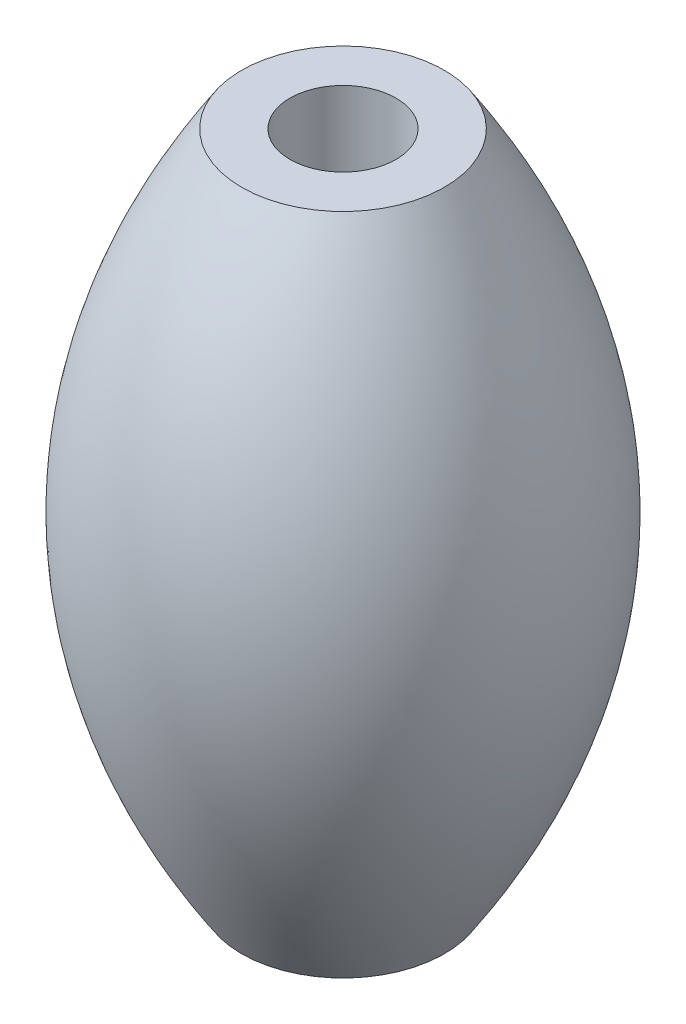
SolidWorks part; units mm, degrees
ref_plane "Front Plane" through (0, 0, 0) normal (0, 0, 1) x (1, 0, 0)
ref_plane "Top Plane" through (0, 0, 0) normal (0, 1, 0) x (1, 0, 0)
ref_plane "Right Plane" through (0, 0, 0) normal (1, 0, 0) x (0, 0, -1)
sketch "Sketch1" plane through (0, 0, 0) normal (0, 0, 1) x (1, 0, 0)
  line L0 (0, 36) -> (0, -27.6486) construction
  line L1 (2.2, 0) -> (2.2, 13.75)
  line L2 (2.2, 0) -> (2.2, -13.75)
  line L3 (2.2, -13.75) -> (4.2, -13.75)
  line L4 (2.2, 13.75) -> (4.2, 13.75)
  spline S0 degree 2 poles (4.2, 13.75) (13.2, 0) (4.2, -13.75) knots 0 0 0 1 1 1
  dimension "D1" = 6.5
  dimension "D2" = 2
  dimension "2.2" = 2.2
  dimension "D3" = 13.75
  dimension "2" = 2
  dimension "D4" = 13.75
revolve "Revolve1" add sketch "Sketch1" angle 360 about L0
